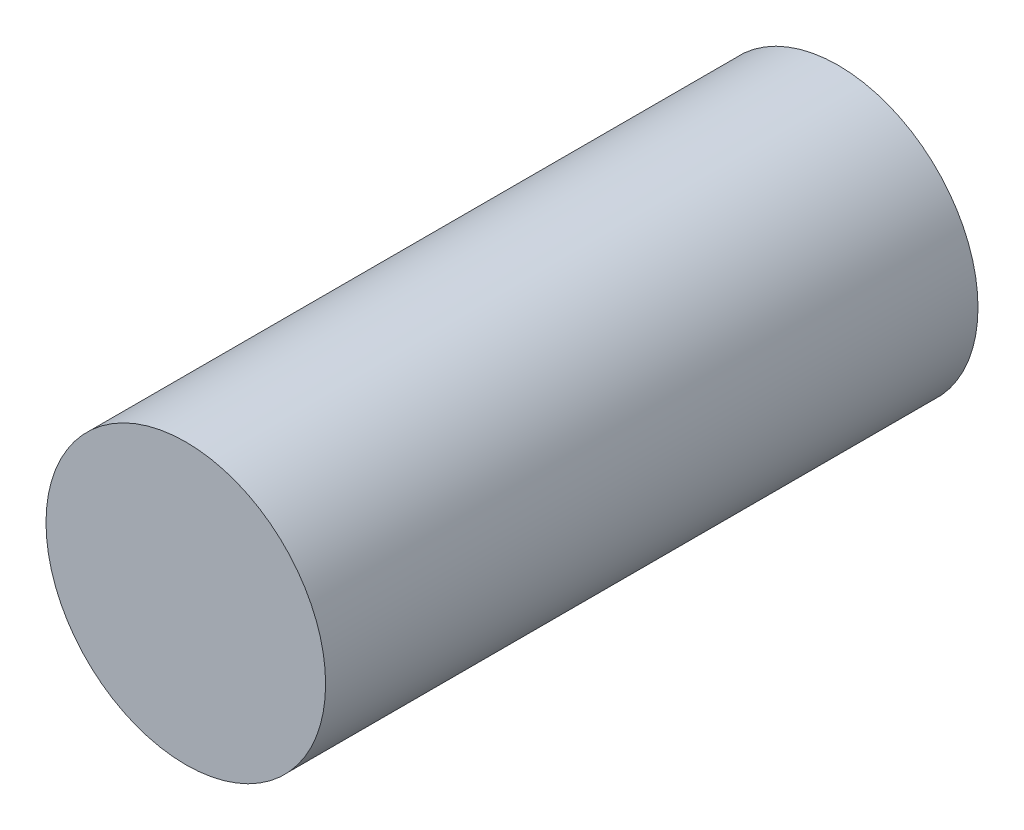
SolidWorks part; units mm, degrees
material "AISI 304"
ref_plane "Front Plane" through (0, 0, 0) normal (0, 0, 1) x (1, 0, 0)
ref_plane "Top Plane" through (0, 0, 0) normal (0, 1, 0) x (1, 0, 0)
ref_plane "Right Plane" through (0, 0, 0) normal (1, 0, 0) x (0, 0, -1)
sketch "Sketch1" plane through (0, 0, 0) normal (0, 0, 1) x (1, 0, 0)
  circle A0 centre (0, 0) radius 3
  dimension "D1" = 6
extrude "Boss-Extrude1" add sketch "Sketch1" along normal blind 14
